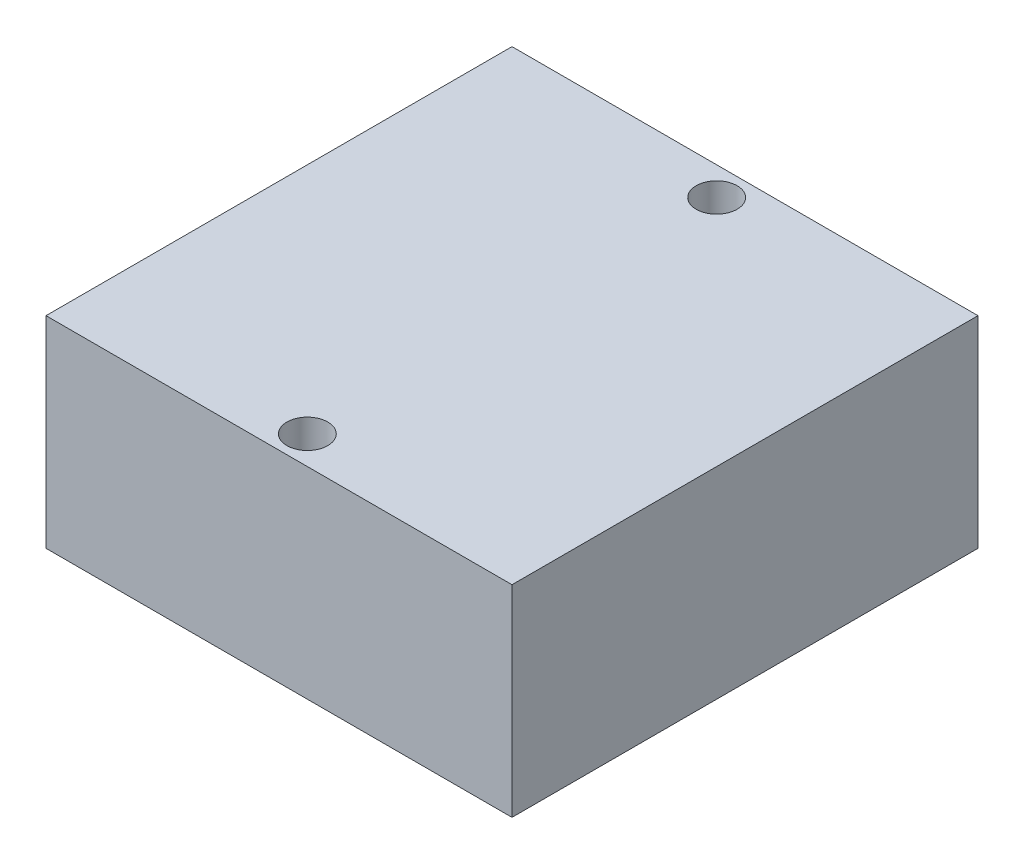
SolidWorks part; units mm, degrees
ref_plane "前视基准面" through (0, 0, 0) normal (0, 0, 1) x (1, 0, 0)
ref_plane "上视基准面" through (0, 0, 0) normal (0, 1, 0) x (1, 0, 0)
ref_plane "右视基准面" through (0, 0, 0) normal (1, 0, 0) x (0, 0, -1)
sketch "草图1" plane through (0, 0, 0) normal (0, 1, 0) x (1, 0, 0)
  line L1 (-37, -37) -> (37, -37)
  line L2 (-37, -37) -> (-37, 37)
  line L3 (-37, 37) -> (37, 37)
  line L4 (37, -37) -> (37, 37)
  line L5 (-37, -37) -> (37, 37) construction
  line L6 (-37, 37) -> (37, -37) construction
  point P0 (0, 0)
  dimension "D1" = 74
  dimension "D2" = 74
extrude "凸台-拉伸1" add sketch "草图1" along normal blind 32
sketch "草图2" plane through (0, 32, 0) normal (0, 1, 0) x (1, 0, 0)
  line L0 (0, 32.5) -> (0, -32.5) construction
  circle A0 centre (0, 32.5) radius 3.25
  circle A1 centre (0, -32.5) radius 3.25
  point P4 (0, 0)
  dimension "D2" = 6.5
  dimension "D1" = 65
extrude "切除-拉伸1" cut sketch "草图2" against normal through all
